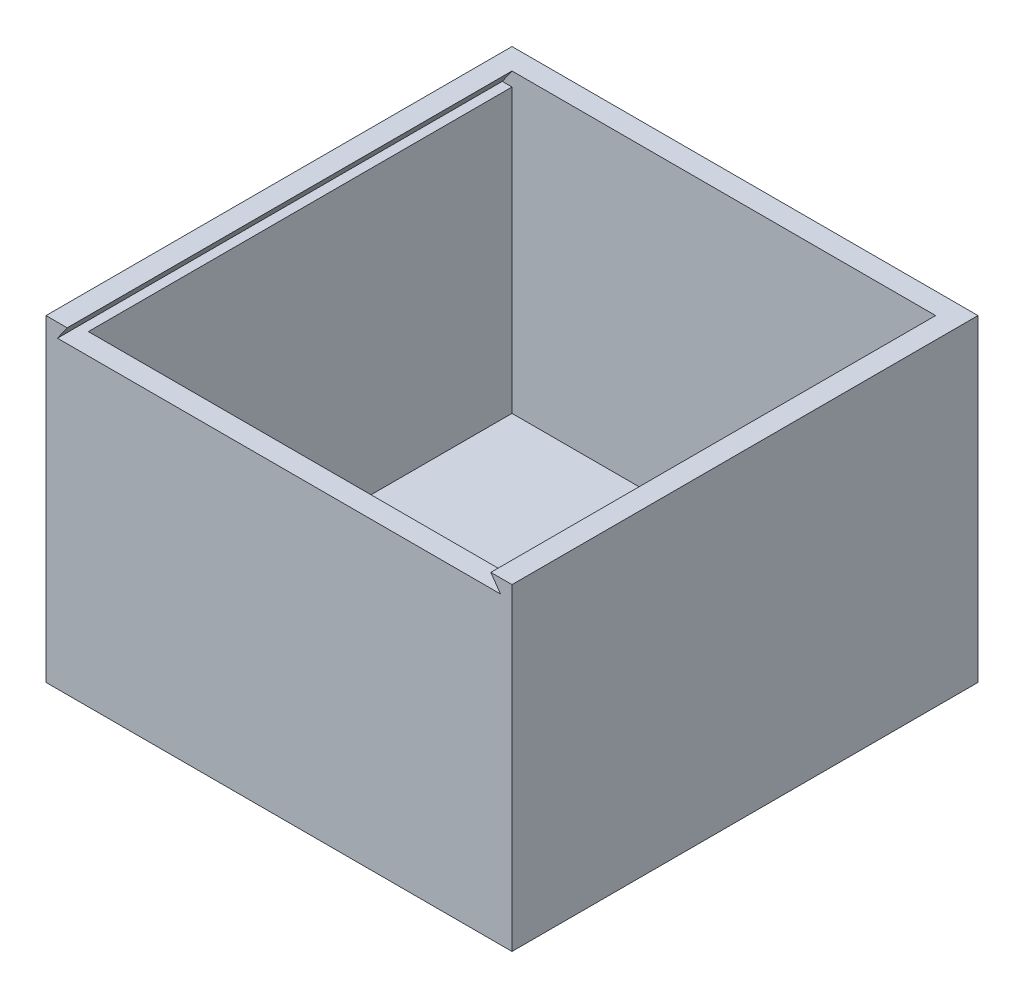
SolidWorks part; units mm, degrees
ref_plane "Front Plane" through (0, 0, 0) normal (0, 0, 1) x (1, 0, 0)
ref_plane "Top Plane" through (0, 0, 0) normal (0, 1, 0) x (1, 0, 0)
ref_plane "Right Plane" through (0, 0, 0) normal (1, 0, 0) x (0, 0, -1)
sketch "Sketch1" plane through (0, 0, 0) normal (0, 1, 0) x (1, 0, 0)
  line L5 (-55, -55) -> (55, -55)
  line L6 (-55, -55) -> (-55, 55)
  line L7 (-55, 55) -> (55, 55)
  line L8 (55, -55) -> (55, 55)
  dimension "D1" = 110
  dimension "D3" = 110
  dimension "D7" = 55
  dimension "D8" = 55
  dimension "D15" = 55
  dimension "D16" = 55
extrude "Boss-Extrude1" add sketch "Sketch1" along normal blind 75
sketch "Sketch2" plane through (0, 75, 0) normal (0, 1, 0) x (1, 0, 0)
  line L0 (-55, 55) -> (-55, -55) construction
  line L1 (-50, -50) -> (50, -50)
  line L2 (-50, -50) -> (-50, 50)
  line L3 (-50, 50) -> (50, 50)
  line L4 (50, -50) -> (50, 50)
  line L5 (55, -55) -> (55, 55) construction
  line L6 (55, 55) -> (-55, 55) construction
  line L7 (-55, -55) -> (55, -55) construction
  dimension "D1" = 5
  dimension "D2" = 5
  dimension "D3" = 5
  dimension "D4" = 5
  dimension "D5" = 100
  dimension "D6" = 100
extrude "Cut-Extrude2" cut sketch "Sketch2" against normal blind 70
sketch "Sketch4" plane through (0, 0, 55) normal (0, 0, 1) x (1, 0, 0)
  line L0 (50, 75) -> (52.2943, 71.7234)
  line L1 (-55, 75) -> (55, 75) construction
  line L2 (-50, 75) -> (-52.2943, 71.7234)
  line L3 (-52.2943, 71.7234) -> (52.2943, 71.7234)
  line L4 (-50, 75) -> (50, 75)
  dimension "D1" = 5
  dimension "D2" = 4
  dimension "D3" = 55
  dimension "D4" = 4
  dimension "D5" = 5
  dimension "D6" = 55
extrude "Cut-Extrude3" cut sketch "Sketch4" against normal up to vertex
